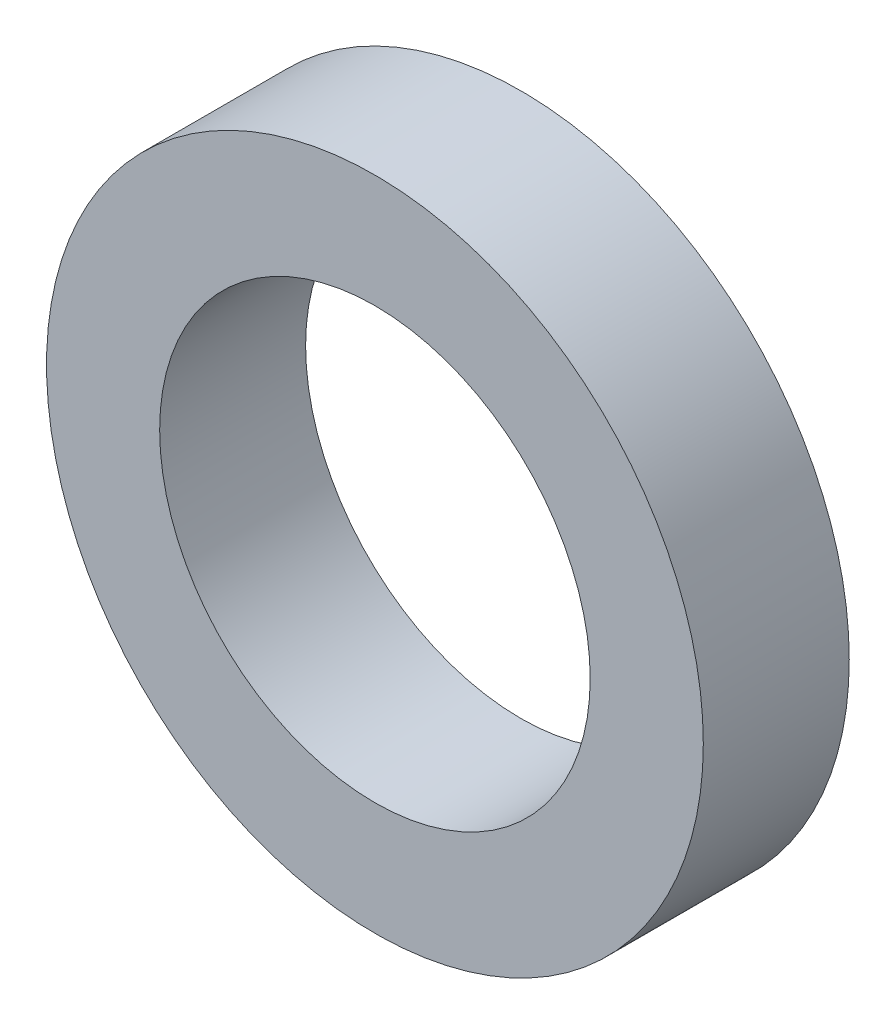
SolidWorks part; units mm, degrees
ref_plane "Front Plane" through (0, 0, 0) normal (0, 0, 1) x (1, 0, 0)
ref_plane "Top Plane" through (0, 0, 0) normal (0, 1, 0) x (1, 0, 0)
ref_plane "Right Plane" through (0, 0, 0) normal (1, 0, 0) x (0, 0, -1)
sketch "Model" plane through (0, 0, 0) normal (0, 0, 1) x (1, 0, 0)
  circle A0 centre (-45, -4) radius 4.5
  circle A1 centre (-45, -4) radius 2.95
extrude "Boss-Extrude1" add sketch "Model" along normal blind 2
